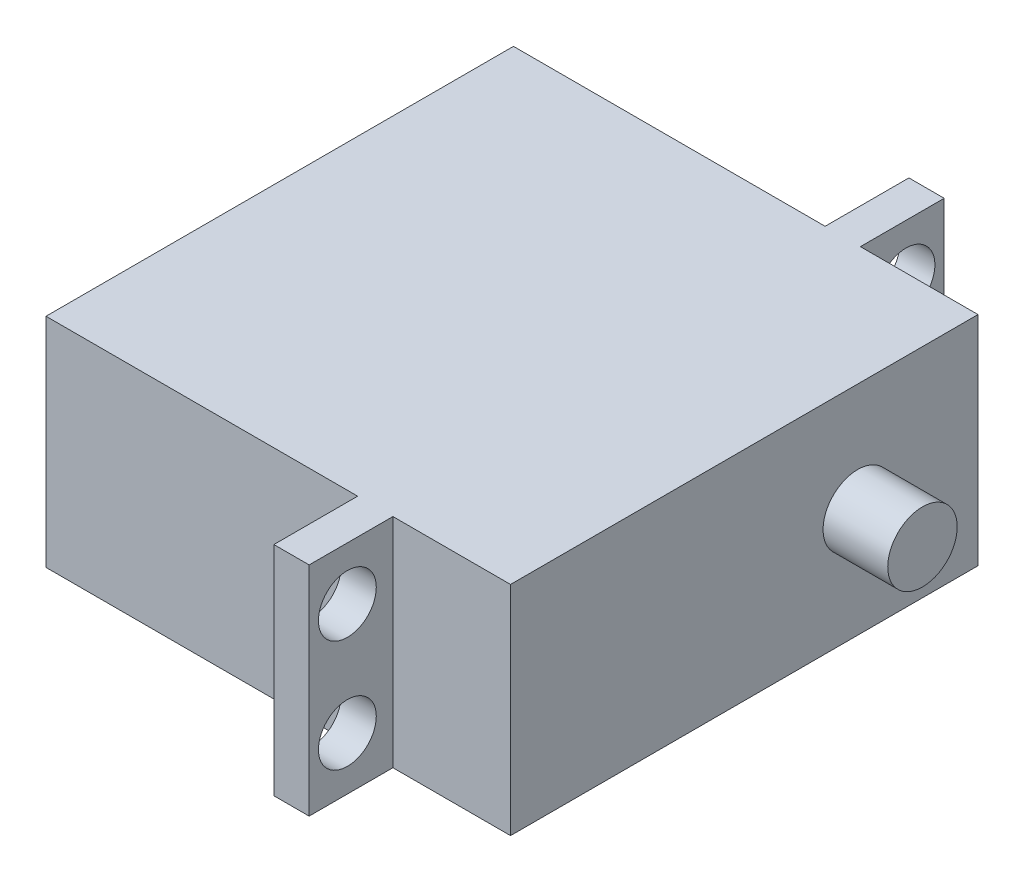
SolidWorks part; units mm, degrees
ref_plane "Front Plane" through (0, 0, 0) normal (0, 0, 1) x (1, 0, 0)
ref_plane "Top Plane" through (0, 0, 0) normal (0, 1, 0) x (1, 0, 0)
ref_plane "Right Plane" through (0, 0, 0) normal (1, 0, 0) x (0, 0, -1)
sketch "Sketch1" plane through (0, 0, 0) normal (1, 0, 0) x (0, 0, -1)
  line L1 (0, 0) -> (-40.386, 0)
  line L2 (0, 0) -> (0, -18.796)
  line L3 (0, -18.796) -> (-40.386, -18.796)
  line L4 (-40.386, 0) -> (-40.386, -18.796)
  dimension "D1" = 40.386
  dimension "D2" = 18.796
extrude "Boss-Extrude1" add sketch "Sketch1" along normal blind 40.132
ref_plane "Plane1" through (26.924, 0, 0) normal (1, 0, 0) x (0, 0, -1)
sketch "Sketch2" plane through (26.924, 0, 0) normal (1, 0, 0) x (0, 0, -1)
  line L0 (-40.386, 0) -> (-40.386, -18.796) construction
  line L1 (-40.386, 0) -> (-47.625, 0)
  line L2 (-40.386, 0) -> (-40.386, -18.796)
  line L3 (-40.386, -18.796) -> (-47.625, -18.796)
  line L4 (-47.625, 0) -> (-47.625, -18.796)
  line L5 (-20.193, 0) -> (-20.193, -18.796) construction
  line L6 (0, 0) -> (-40.386, 0) construction
  line L7 (-40.386, -18.796) -> (0, -18.796) construction
  line L8 (0, -18.796) -> (0, 0) construction
  line L9 (0, 0) -> (7.239, 0)
  line L10 (0, 0) -> (0, -18.796)
  line L11 (0, -18.796) -> (7.239, -18.796)
  line L12 (7.239, 0) -> (7.239, -18.796)
  line L13 (-47.625, -9.398) -> (-40.386, -9.398) construction
  line L14 (0, -9.398) -> (7.239, -9.398) construction
  line L15 (-44.323, 0) -> (-44.323, -4.572) construction
  line L16 (-44.323, -4.572) -> (-44.323, -9.398) construction
  line L17 (-44.323, -14.224) -> (-44.323, -18.796) construction
  line L18 (3.937, -14.224) -> (3.937, -18.796) construction
  line L19 (3.937, -4.572) -> (3.937, -14.224) construction
  line L20 (3.937, 0) -> (3.937, -4.572) construction
  line L21 (-44.323, -9.398) -> (-44.323, -14.224) construction
  circle A0 centre (-44.323, -4.572) radius 2.5
  circle A1 centre (-44.323, -14.224) radius 2.5
  circle A2 centre (3.937, -4.572) radius 2.5
  circle A3 centre (3.937, -14.224) radius 2.5
  dimension "D4" = 5
  dimension "D1" = 54.864
  dimension "D2" = 9.652
  dimension "D3" = 48.26
extrude "Boss-Extrude2" add sketch "Sketch2" along normal blind 3.048
sketch "Sketch3" plane through (40.132, 0, 0) normal (1, 0, 0) x (0, 0, -1)
  line L0 (-10.386, -9.398) -> (-40.386, -9.398) construction
  line L1 (-40.386, -18.796) -> (-40.386, 0) construction
  circle A0 centre (-10.386, -9.398) radius 3
  dimension "D1" = 6
  dimension "D2" = 30
extrude "Boss-Extrude3" add sketch "Sketch3" along normal blind 5.588
